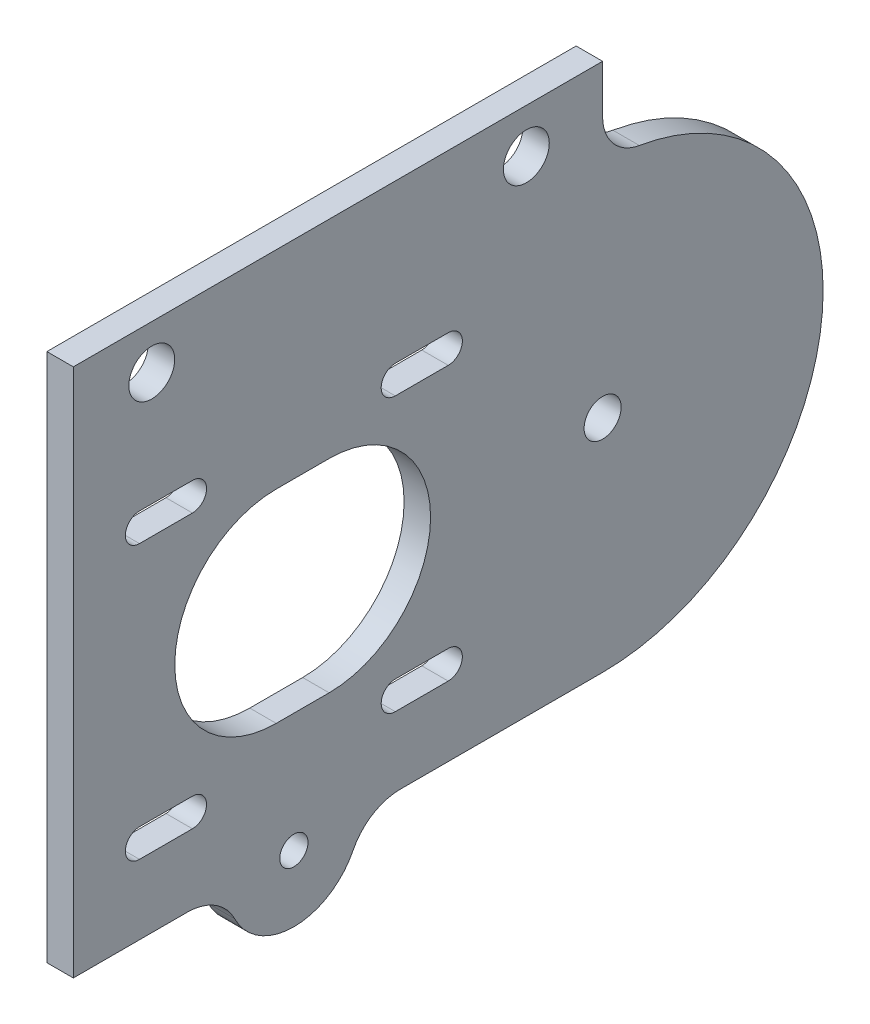
SolidWorks part; units mm, degrees
ref_plane "Front Plane" through (0, 0, 0) normal (0, 0, 1) x (1, 0, 0)
ref_plane "Top Plane" through (0, 0, 0) normal (0, 1, 0) x (1, 0, 0)
ref_plane "Right Plane" through (0, 0, 0) normal (1, 0, 0) x (0, 0, -1)
sketch "Sketch1" plane through (0, 0, 0) normal (1, 0, 0) x (0, 0, -1)
  line L0 (-25, 15.5) -> (25, 15.5) construction
  line L1 (-25, 25) -> (25, 25)
  line L2 (-25, 25) -> (-25, -25)
  line L3 (-25, -25) -> (25, -25)
  line L4 (25, 25) -> (25, -25)
  line L5 (-25, 25) -> (25, -25) construction
  line L6 (-25, -25) -> (25, 25) construction
  line L7 (-25, 0) -> (25, 0) construction
  line L8 (35, 25) -> (25, 25)
  line L9 (25, -25) -> (35, -25)
  line L10 (-17.5, 15.5) -> (-11.5, 15.5) construction
  line L11 (-17.5, 17.1) -> (-11.5, 17.1)
  line L12 (-17.5, 13.9) -> (-11.5, 13.9)
  line L13 (-15.5, 25) -> (-15.5, -25) construction
  line L14 (0, 0) -> (0, 25) construction
  line L15 (17.5, 15.5) -> (11.5, 15.5) construction
  line L16 (17.5, 17.1) -> (11.5, 17.1)
  line L17 (17.5, 13.9) -> (11.5, 13.9)
  line L18 (17.5, -15.5) -> (11.5, -15.5) construction
  line L19 (17.5, -17.1) -> (11.5, -17.1)
  line L20 (17.5, -13.9) -> (11.5, -13.9)
  line L21 (-17.5, -15.5) -> (-11.5, -15.5) construction
  line L22 (-17.5, -17.1) -> (-11.5, -17.1)
  line L23 (-17.5, -13.9) -> (-11.5, -13.9)
  line L24 (-2, 0) -> (4, 0) construction
  line L25 (-2, 11.5) -> (4, 11.5)
  line L26 (-2, -11.5) -> (4, -11.5)
  arc A1 (-17.5, 17.1) -> (-17.5, 13.9) centre (-17.5, 15.5) ccw
  arc A2 (-11.5, 13.9) -> (-11.5, 17.1) centre (-11.5, 15.5) ccw
  arc A3 (17.5, 17.1) -> (17.5, 13.9) centre (17.5, 15.5) cw
  arc A4 (11.5, 13.9) -> (11.5, 17.1) centre (11.5, 15.5) cw
  circle A5 centre (35, 0) radius 25
  circle A6 centre (35, 0) radius 2.1
  arc A7 (17.5, -17.1) -> (17.5, -13.9) centre (17.5, -15.5) ccw
  arc A8 (11.5, -13.9) -> (11.5, -17.1) centre (11.5, -15.5) ccw
  arc A9 (-17.5, -17.1) -> (-17.5, -13.9) centre (-17.5, -15.5) cw
  arc A10 (-11.5, -13.9) -> (-11.5, -17.1) centre (-11.5, -15.5) cw
  arc A11 (-2, 11.5) -> (-2, -11.5) centre (-2, 0) ccw
  arc A12 (4, -11.5) -> (4, 11.5) centre (4, 0) ccw
  point P0 (0, 0)
  point P12 (-14.5, 15.5)
  point P19 (14.5, 15.5)
  point P36 (14.5, -15.5)
  point P43 (-14.5, -15.5)
  point P50 (1, 0)
  dimension "D4" = 1.6
  dimension "D5" = 6
  dimension "D6" = 4
  dimension "D8" = 4.2
  dimension "D10" = 31
  dimension "D13" = 11.5
  dimension "D2" = 50
  dimension "D3" = 50
  dimension "D9" = 15.5
  dimension "D11" = 4
  dimension "D12" = 6
extrude "Boss-Extrude2" add sketch "Sketch1" along normal blind 3
sketch "Sketch2" plane through (3, 0, 0) normal (1, 0, 0) x (0, 0, -1)
  circle A1 centre (35, 0) radius 2.1 construction
  circle A5 centre (0, -24.98) radius 7.5
  dimension "D1" = 35
  dimension "D8" = 15
extrude "Boss-Extrude3" add sketch "Sketch2" against normal blind 3
sketch "Sketch3" plane through (3, 0, 0) normal (1, 0, 0) x (0, 0, -1)
  line L0 (35, 25) -> (35, 35)
  line L1 (35, 35) -> (-25, 35)
  line L2 (-25, 25) -> (-25, 35)
  line L3 (35, 25) -> (-25, 25)
  line L4 (-25, 30) -> (35, 30) construction
  circle A0 centre (-16.1058, 30) radius 2.6
  circle A1 centre (26.3561, 30) radius 2.6
  dimension "D1" = 5.2
  dimension "D2" = 5.2
  dimension "D3" = 10
extrude "Boss-Extrude4" add sketch "Sketch3" against normal blind 3
fillet "Fillet3" radius 5 1 edges at (1.5, 25, -35)
sketch "Sketch4" plane through (0, 0, 0) normal (-1, 0, 0) x (0, 0, 1)
  circle A0 centre (0, -24.98) radius 1.6
  dimension "D1" = 3.2
extrude "Cut-Extrude1" cut sketch "Sketch4" against normal through all
fillet "Fillet4" radius 6 2 edges at (1.5, -25, 7.5) (1.5, -25, -7.5)
